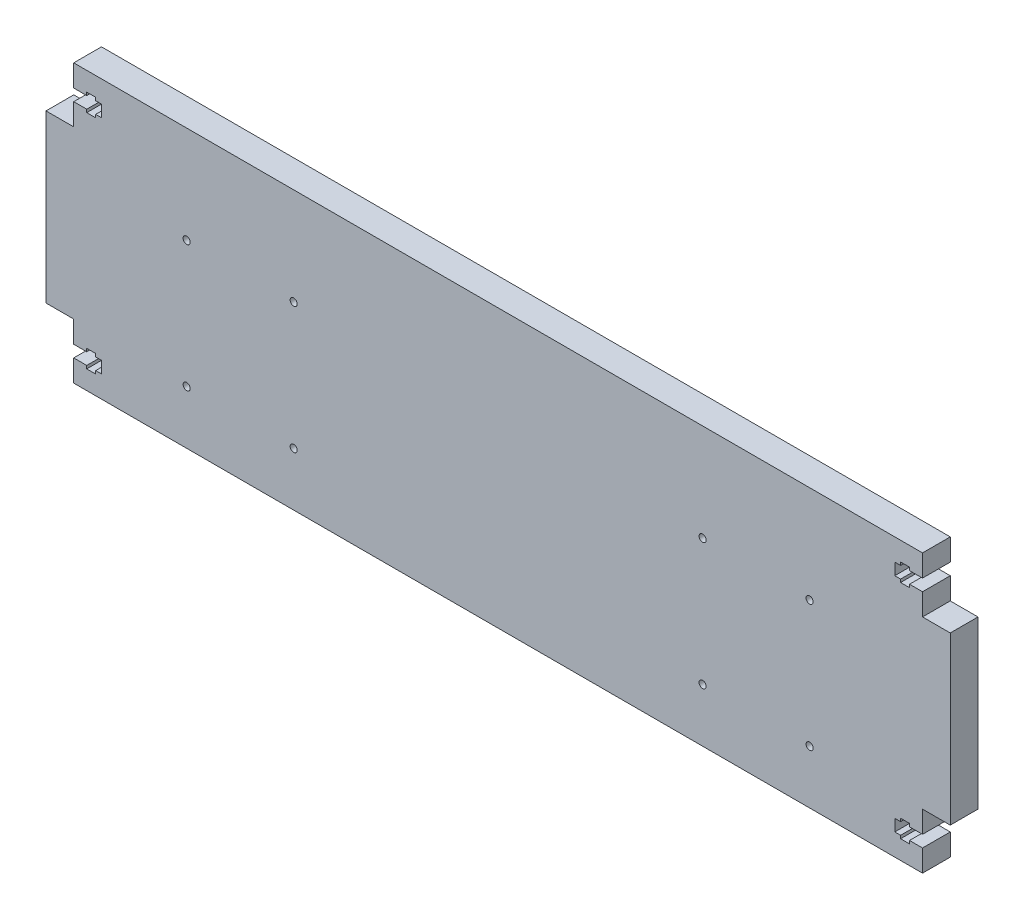
SolidWorks part; units mm, degrees
material "Pine"
ref_plane "Front Plane" through (0, 0, 0) normal (0, 0, 1) x (1, 0, 0)
ref_plane "Top Plane" through (0, 0, 0) normal (0, 1, 0) x (1, 0, 0)
ref_plane "Right Plane" through (0, 0, 0) normal (1, 0, 0) x (0, 0, -1)
sketch "Sketch1" plane through (0, 0, 0) normal (0, 0, 1) x (1, 0, 0)
  line L0 (0, 0) -> (0, 50000) construction
  line L1 (194.31, -63.5) -> (-194.31, -63.5)
  line L2 (207.01, -38.1) -> (207.01, 38.1)
  line L3 (194.31, 63.5) -> (-194.31, 63.5)
  line L4 (-207.01, -38.1) -> (-207.01, 38.1)
  line L7 (-207.01, 38.1) -> (-194.31, 38.1)
  line L10 (-194.31, 38.1) -> (-194.31, 63.5)
  line L11 (0, 0) -> (50000, 0) construction
  line L12 (-194.31, -38.1) -> (-194.31, -63.5)
  line L13 (-207.01, -38.1) -> (-194.31, -38.1)
  line L14 (194.31, 38.1) -> (194.31, 63.5)
  line L15 (207.01, 38.1) -> (194.31, 38.1)
  line L16 (207.01, -38.1) -> (194.31, -38.1)
  line L17 (194.31, -38.1) -> (194.31, -63.5)
  point P0 (0, 0)
  dimension "D1" = 127
  dimension "D2" = 414.02
  dimension "D3" = 12.7
  dimension "D4" = 25.4
extrude "Boss-Extrude1" add sketch "Sketch1" along normal blind 12.7
sketch "Sketch2" plane through (0, 0, 12.7) normal (0, 0, 1) x (1, 0, 0)
  line L0 (-194.31, 63.5) -> (-194.31, 38.1) construction
  line L1 (-194.31, 53.5) -> (-181.61, 53.5)
  line L2 (-194.31, 53.5) -> (-194.31, 48.1)
  line L3 (-194.31, 48.1) -> (-181.61, 48.1)
  line L4 (-181.61, 53.5) -> (-181.61, 48.1)
  line L5 (-181.61, 50.8) -> (-194.31, 50.8) construction
  line L6 (-194.31, 63.5) -> (-194.31, 38.1) construction
  line L7 (0, 0) -> (-50000, 0) construction
  line L8 (0, 0) -> (0, 50000) construction
  line L9 (-194.31, -63.5) -> (-194.31, -38.1) construction
  line L10 (-181.61, -50.8) -> (-194.31, -50.8) construction
  line L11 (-181.61, -53.5) -> (-181.61, -48.1)
  line L12 (-194.31, -48.1) -> (-181.61, -48.1)
  line L13 (-194.31, -53.5) -> (-194.31, -48.1)
  line L14 (-194.31, -53.5) -> (-181.61, -53.5)
  line L15 (181.61, -50.8) -> (194.31, -50.8) construction
  line L16 (194.31, -63.5) -> (194.31, -38.1) construction
  line L17 (194.31, 63.5) -> (194.31, 38.1) construction
  line L18 (181.61, 50.8) -> (194.31, 50.8) construction
  line L19 (194.31, -53.5) -> (181.61, -53.5)
  line L20 (194.31, -53.5) -> (194.31, -48.1)
  line L21 (194.31, -48.1) -> (181.61, -48.1)
  line L22 (181.61, -53.5) -> (181.61, -48.1)
  line L23 (181.61, 53.5) -> (181.61, 48.1)
  line L24 (194.31, 48.1) -> (181.61, 48.1)
  line L25 (194.31, 53.5) -> (194.31, 48.1)
  line L26 (194.31, 53.5) -> (181.61, 53.5)
  dimension "D1" = 5.4
  dimension "D2" = 12.7
extrude "m5 shaft" cut sketch "Sketch2" against normal up to next
sketch "Sketch3" plane through (0, 0, 12.7) normal (0, 0, 1) x (1, 0, 0)
  line L0 (-181.61, 50.8) -> (-194.31, 50.8) construction
  line L1 (-181.61, 48.1) -> (-181.61, 53.5) construction
  line L2 (0, 0) -> (0, 50000) construction
  line L3 (-184.26, 46.725) -> (-188.36, 46.725)
  line L4 (-184.26, 46.725) -> (-184.26, 54.875)
  line L5 (-184.26, 54.875) -> (-188.36, 54.875)
  line L6 (-188.36, 46.725) -> (-188.36, 54.875)
  line L7 (-184.26, 46.725) -> (-188.36, 54.875) construction
  line L8 (-184.26, 54.875) -> (-188.36, 46.725) construction
  line L9 (194.31, 63.5) -> (-194.31, 63.5) construction
  line L10 (0, 0) -> (-50000, 0) construction
  line L11 (-184.26, -54.875) -> (-188.36, -46.725) construction
  line L12 (-184.26, -46.725) -> (-188.36, -54.875) construction
  line L13 (-181.61, -50.8) -> (-194.31, -50.8) construction
  line L14 (-188.36, -46.725) -> (-188.36, -54.875)
  line L15 (-184.26, -54.875) -> (-188.36, -54.875)
  line L16 (-184.26, -46.725) -> (-184.26, -54.875)
  line L17 (-184.26, -46.725) -> (-188.36, -46.725)
  line L18 (181.61, -50.8) -> (194.31, -50.8) construction
  line L19 (184.26, -46.725) -> (188.36, -54.875) construction
  line L20 (184.26, -54.875) -> (188.36, -46.725) construction
  line L21 (184.26, -46.725) -> (188.36, -46.725)
  line L22 (184.26, -46.725) -> (184.26, -54.875)
  line L23 (184.26, -54.875) -> (188.36, -54.875)
  line L24 (188.36, -46.725) -> (188.36, -54.875)
  line L25 (184.26, 54.875) -> (188.36, 46.725) construction
  line L26 (184.26, 46.725) -> (188.36, 54.875) construction
  line L27 (181.61, 50.8) -> (194.31, 50.8) construction
  line L28 (188.36, 46.725) -> (188.36, 54.875)
  line L29 (184.26, 54.875) -> (188.36, 54.875)
  line L30 (184.26, 46.725) -> (184.26, 54.875)
  line L31 (184.26, 46.725) -> (188.36, 46.725)
  point P4 (-186.31, 50.8)
  point P14 (0, 63.5)
  point P23 (-186.31, -50.8)
  point P30 (186.31, -50.8)
  point P37 (186.31, 50.8)
  dimension "D1" = 12.7
  dimension "D2" = 8
  dimension "D3" = 4.1
  dimension "D4" = 8.15
extrude "m5 nut" cut sketch "Sketch3" against normal up to next
sketch "Sketch4" plane through (0, 0, 12.7) normal (0, 0, 1) x (1, 0, 0)
  line L0 (-207.01, 38.1) -> (-207.01, -38.1) construction
  line L1 (-166.37, -12.7) -> (-153.797, -12.7)
  line L2 (-166.37, -12.7) -> (-166.37, -25.273)
  line L3 (-166.37, -25.273) -> (-153.797, -25.273)
  line L4 (-153.797, -12.7) -> (-153.797, -25.273)
  line L5 (-194.31, -63.5) -> (194.31, -63.5) construction
  line L6 (0, 0) -> (0, 50000) construction
  line L7 (153.797, -12.7) -> (153.797, -25.273)
  line L8 (166.37, -25.273) -> (153.797, -25.273)
  line L9 (166.37, -12.7) -> (166.37, -25.273)
  line L10 (166.37, -12.7) -> (153.797, -12.7)
  line L11 (-160.0835, -25.273) -> (-160.0835, -34.163) construction
  line L12 (160.0835, -25.273) -> (160.0835, -34.163) construction
  line L13 (-160.0835, -12.7) -> (-160.0835, -6.35) construction
  circle A0 centre (-160.0835, -34.163) radius 1.65
  circle A1 centre (160.0835, -34.163) radius 1.65
  circle A2 centre (-160.0835, -6.35) radius 1.65
  circle A3 centre (160.0835, -6.35) radius 1.65
  dimension "D6" = 3.3
  dimension "D1" = 12.573
  dimension "D2" = 12.573
  dimension "D3" = 40.64
  dimension "D4" = 50.8
  dimension "D5" = 8.89
  dimension "D7" = 6.35
sketch "Sketch5" plane through (0, 0, 12.7) normal (0, 0, 1) x (1, 0, 0)
  line L1 (-142.61, 19) -> (-93.61, 19) construction
  line L2 (-142.61, 19) -> (-142.61, -39) construction
  line L3 (-142.61, -39) -> (-93.61, -39) construction
  line L4 (-93.61, 19) -> (-93.61, -39) construction
  line L5 (-146.11, 42.5) -> (-90.11, 42.5) construction
  line L6 (-146.11, 42.5) -> (-146.11, -42.5) construction
  line L7 (-146.11, -42.5) -> (-90.11, -42.5) construction
  line L8 (-90.11, 42.5) -> (-90.11, -42.5) construction
  line L9 (-146.11, 42.5) -> (-90.11, -42.5) construction
  line L10 (-146.11, -42.5) -> (-90.11, 42.5) construction
  line L11 (0, 0) -> (-50000, 0) construction
  line L12 (-194.31, -38.1) -> (-194.31, -48.1) construction
  line L13 (0, 0) -> (0, -50000) construction
  line L14 (-194.31, -63.5) -> (194.31, -63.5) construction
  line L15 (146.11, -42.5) -> (90.11, 42.5) construction
  line L16 (146.11, 42.5) -> (90.11, -42.5) construction
  line L17 (90.11, 42.5) -> (90.11, -42.5) construction
  line L18 (146.11, -42.5) -> (90.11, -42.5) construction
  line L19 (146.11, 42.5) -> (146.11, -42.5) construction
  line L20 (146.11, 42.5) -> (90.11, 42.5) construction
  line L21 (93.61, 19) -> (93.61, -39) construction
  line L22 (142.61, -39) -> (93.61, -39) construction
  line L23 (142.61, 19) -> (142.61, -39) construction
  line L24 (142.61, 19) -> (93.61, 19) construction
  circle A0 centre (-142.61, 19) radius 1.625
  circle A1 centre (-93.61, 19) radius 1.625
  circle A2 centre (-93.61, -39) radius 1.625
  circle A3 centre (-142.61, -39) radius 1.625
  circle A4 centre (142.61, -39) radius 1.625
  circle A5 centre (93.61, -39) radius 1.625
  circle A6 centre (93.61, 19) radius 1.625
  circle A7 centre (142.61, 19) radius 1.625
  point P12 (-118.11, 0)
  point P22 (0, -63.5)
  point P35 (118.11, 0)
  dimension "D1" = 3.25
  dimension "D2" = 49
  dimension "D3" = 58
  dimension "D4" = 3.5
  dimension "D5" = 3.5
  dimension "D6" = 56
  dimension "D7" = 85
  dimension "D8" = 76.2
extrude "rasberry pi holes" cut sketch "Sketch5" against normal up to next
